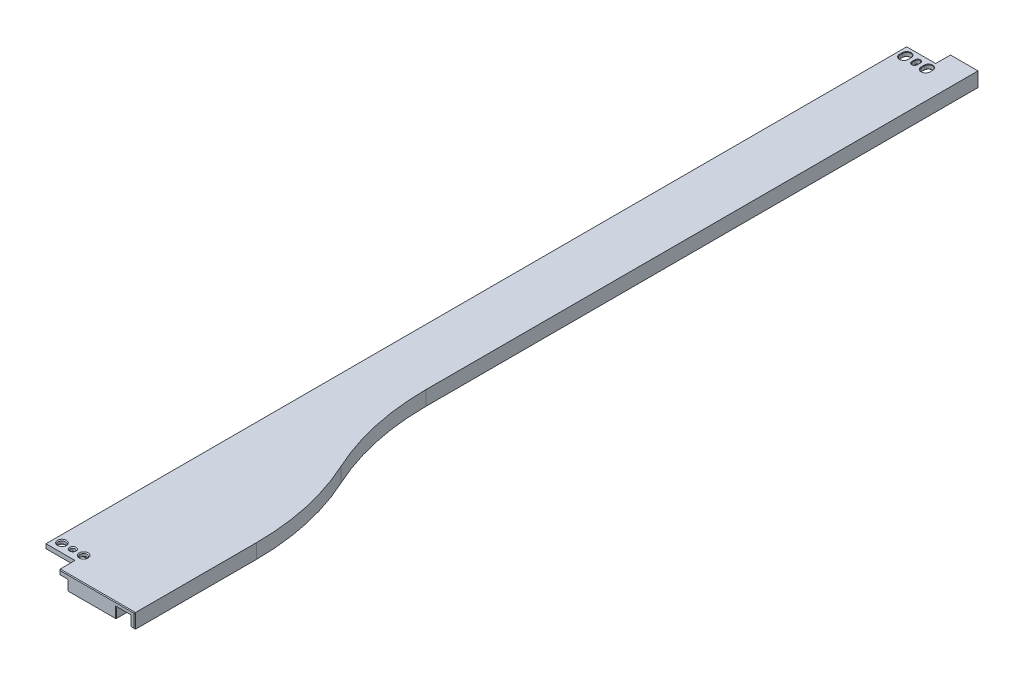
SolidWorks part; units mm, degrees
material "6061 Alloy"
ref_plane "Front" through (0, 0, 0) normal (0, 0, 1) x (1, 0, 0)
ref_plane "Top" through (0, 0, 0) normal (0, 1, 0) x (1, 0, 0)
ref_plane "Right" through (0, 0, 0) normal (1, 0, 0) x (0, 0, -1)
sketch "Sketch1" plane through (0, 0, 0) normal (0, 1, 0) x (1, 0, 0)
  line L0 (0, 0) -> (0, 77.3682) construction
  line L1 (0, 0) -> (-68.6698, 0) construction
  line L2 (-69.1, 0) -> (-69.1, 40) construction
  line L3 (-93.1, 190) -> (-93.1, 840) construction
  line L4 (-126.1, 990) -> (-126.1, 2194) construction
  line L5 (-165.1, 2194) -> (-165.1, 0) construction
  line L6 (-165.1, 2194) -> (-126.1, 2194) construction
  line L7 (-165.1, 0) -> (-69.1, 0) construction
  line L8 (-462.2814, 755.9) -> (800.8337, 755.9) construction
  line L9 (-93.1, 755.6) -> (-145.1, 755.6) construction
  line L10 (-145.1, 755.6) -> (-145.1, 744.9) construction
  line L11 (-145.1, 744.9) -> (-165.1, 744.9) construction
  line L12 (-450.7799, 139.9) -> (404.4044, 139.9) construction
  line L13 (-165.1, 158.4) -> (-145.1, 158.4) construction
  line L14 (-145.1, 158.4) -> (-145.1, 121.4) construction
  line L15 (-145.1, 121.4) -> (-165.1, 121.4) construction
  line L16 (-165.1, 121.4) -> (-165.1, 0) construction
  line L17 (-165.1, 744.9) -> (-165.1, 158.4) construction
  line L18 (-93.1, 755.6) -> (-93.1, 190) construction
  line L19 (-752.0446, 1371.9) -> (535.2926, 1371.9) construction
  line L20 (-878.4617, 1987.9) -> (588.9463, 1987.9) construction
  line L21 (-93.1, 756.2) -> (-145.1, 756.2)
  line L22 (-145.1, 756.2) -> (-145.1, 766.9)
  line L23 (-145.1, 766.9) -> (-165.1, 766.9)
  line L24 (-107.1553, 756.2) -> (-107.1553, 755.6) construction
  line L25 (-144.4764, 1372.2) -> (-144.4764, 1371.6) construction
  line L26 (-126.1, 1371.6) -> (-145.1, 1371.6)
  line L27 (-165.1, 1360.9) -> (-165.1, 766.9)
  line L28 (-126.1, 1371.6) -> (-126.1, 990)
  line L29 (-93.1, 756.2) -> (-93.1, 840)
  line L30 (-145.1, 1371.6) -> (-145.1, 1360.9)
  line L31 (-145.1, 1360.9) -> (-165.1, 1360.9)
  arc A0 (-93.1, 190) -> (-81.1, 115) centre (147.275, 190) ccw construction
  arc A1 (-81.1, 115) -> (-69.1, 40) centre (-309.475, 40) cw construction
  arc A2 (-126.1, 990) -> (-109.6, 915) centre (52.6045, 990) ccw construction
  arc A3 (-109.6, 915) -> (-93.1, 840) centre (-271.8045, 840) cw construction
  arc A4 (-126.1, 990) -> (-109.6, 915) centre (52.6045, 990) ccw
  arc A5 (-109.6, 915) -> (-93.1, 840) centre (-271.8045, 840) cw
  point P28 (-145.1, 139.9)
  point P41 (-107.1553, 755.9)
  point P44 (-144.4764, 1371.9)
  dimension "D1" = 2194
  dimension "D2" = 39
  dimension "D3" = 165.1
  dimension "D4" = 24
  dimension "D5" = 33
  dimension "D6" = 40
  dimension "D7" = 150
  dimension "D8" = 840
  dimension "D9" = 150
  dimension "D10" = 755.9
  dimension "D11" = 0.3
  dimension "D12" = 11
  dimension "D13" = 20
  dimension "D14" = 139.9
  dimension "D15" = 37
  dimension "D16" = 616
  dimension "D17" = 616
extrude "Extrude1" add sketch "Sketch1" against normal blind 10
sketch "Sketch4" plane through (0, -10, 0) normal (0, -1, 0) x (1, 0, 0)
  line L0 (-83.1, 0) -> (-83.1, -40) construction
  line L1 (-107.1, -190) -> (-107.1, -190.4) construction
  line L2 (-100.1, -755.6) -> (-107.1, -755.6) construction
  line L3 (-107.1, -755.6) -> (-107.1, -707.4) construction
  line L6 (-76.1, 0) -> (-76.1, -40) construction
  line L7 (-100.1, -190) -> (-100.1, -755.6) construction
  line L8 (-107.1, -707.4) -> (-165.1, -707.4) construction
  line L10 (-165.1, -707.4) -> (-165.1, -190.4) construction
  line L11 (-165.1, -190.4) -> (-107.1, -190.4) construction
  line L13 (-83.1, 0) -> (-76.1, 0) construction
  line L18 (-165.1, -789.4) -> (-106.1, -789.4)
  line L21 (-165.1, -1360.9) -> (-165.1, -766.9) construction
  line L22 (-96.1, -756.2) -> (-96.1, -840)
  line L23 (-129.1, -990) -> (-129.1, -1371.6)
  line L24 (-96.1, -756.2) -> (-96.1, -840)
  line L25 (-129.1, -990) -> (-129.1, -1371.6)
  line L26 (-106.1, -789.4) -> (-106.1, -756.2)
  line L27 (-96.1, -756.2) -> (-106.1, -756.2)
  line L28 (-93.1, -756.2) -> (-145.1, -756.2) construction
  line L30 (-145.1, -766.9) -> (-165.1, -766.9) construction
  line L31 (-129.1, -1371.6) -> (-139.1, -1371.6)
  line L32 (-139.1, -1371.6) -> (-139.1, -1338.4)
  line L33 (-139.1, -1338.4) -> (-165.1, -1338.4)
  line L34 (-145.1, -1360.9) -> (-165.1, -1360.9) construction
  line L35 (-165.1, -789.4) -> (-165.1, -1338.4)
  arc A0 (-94.6008, -111.8799) -> (-83.1, -40) centre (-313.475, -40) ccw construction
  arc A1 (-94.6008, -111.8799) -> (-107.1, -190) centre (143.275, -190) ccw construction
  arc A6 (-87.9502, -114.064) -> (-76.1, -40) centre (-313.475, -40) ccw construction
  arc A7 (-87.9502, -114.064) -> (-100.1, -190) centre (143.275, -190) ccw construction
  arc A13 (-112.323, -913.7409) -> (-96.1, -840) centre (-271.8045, -840) ccw
  arc A14 (-112.323, -913.7409) -> (-129.1, -990) centre (52.6045, -990) ccw
  arc A15 (-112.323, -913.7409) -> (-96.1, -840) centre (-271.8045, -840) ccw
  arc A16 (-112.323, -913.7409) -> (-129.1, -990) centre (52.6045, -990) ccw
  dimension "D3" = 3
  dimension "D6" = 7
  dimension "D7" = 10
  dimension "D8" = 22.5
  dimension "D9" = 10
  dimension "D10" = 22.5
  dimension "D2" = 7
extrude "Extrude2" cut sketch "Sketch4" against normal offset from surface (7 mm away) 3 up to face at (-132.6, 0, -1023.2909)
sketch "Sketch5" plane through (0, -10, 0) normal (0, -1, 0) x (1, 0, 0)
  line L1 (-165.1, -106.4) -> (-139.1, -106.4) construction
  line L2 (-165.1, -106.4) -> (-165.1, -173.4) construction
  line L3 (-165.1, -173.4) -> (-139.1, -173.4) construction
  line L4 (-139.1, -106.4) -> (-139.1, -173.4) construction
  line L7 (-165.1, -722.4) -> (-139.1, -722.4) construction
  line L8 (-165.1, -722.4) -> (-165.1, -737.4) construction
  line L9 (-165.1, -737.4) -> (-139.1, -737.4) construction
  line L10 (-139.1, -722.4) -> (-139.1, -737.4) construction
  line L11 (-145.1, -766.9) -> (-145.1, -756.2) construction
  line L12 (-165.1, -766.9) -> (-145.1, -766.9)
  line L13 (-165.1, -766.9) -> (-165.1, -781.9)
  line L14 (-165.1, -781.9) -> (-145.1, -781.9)
  line L15 (-145.1, -766.9) -> (-145.1, -781.9)
  line L16 (-139.1, -1338.4) -> (-139.1, -1371.6) construction
  line L17 (-165.1, -1360.9) -> (-139.1, -1360.9)
  line L18 (-165.1, -1360.9) -> (-165.1, -1345.9)
  line L19 (-165.1, -1345.9) -> (-139.1, -1345.9)
  line L20 (-139.1, -1360.9) -> (-139.1, -1345.9)
  dimension "D1" = 67
  dimension "D2" = 15
  dimension "D3" = 15
  dimension "D4" = 15
extrude "Extrude3" cut sketch "Sketch5" against normal up to surface (7 mm away) up to face at (-125.7691, -3, -1023.1737)
sketch "Sketch15" plane through (0, -10, 0) normal (0, -1, 0) x (1, 0, 0)
  line L0 (-145.1, -781.9) -> (-165.1, -781.9) construction
  line L1 (-139.1, -1360.9) -> (-145.1, -1360.9)
  line L2 (-139.1, -1360.9) -> (-139.1, -1371.6)
  line L3 (-139.1, -1371.6) -> (-145.1, -1371.6)
  line L4 (-145.1, -1360.9) -> (-145.1, -1371.6)
  line L5 (-145.1, -756.2) -> (-139.1, -756.2)
  line L6 (-145.1, -756.2) -> (-145.1, -781.9)
  line L7 (-145.1, -781.9) -> (-139.1, -781.9)
  line L8 (-139.1, -756.2) -> (-139.1, -781.9)
extrude "Extrude9" cut sketch "Sketch15" against normal up to surface (7 mm away) up to face at (-133.56, -3, -1126.8382)
sketch "Sketch8" plane through (0, -3, 0) normal (0, -1, 0) x (1, 0, 0)
  line L0 (-450.7799, -139.9) -> (404.4044, -139.9) construction
  line L1 (-161.3213, -115.4) -> (-146.3213, -115.4) construction
  line L2 (-161.3213, -115.4) -> (-161.3213, -164.4) construction
  line L3 (-161.3213, -164.4) -> (-146.3213, -164.4) construction
  line L4 (-146.3213, -115.4) -> (-146.3213, -164.4) construction
  line L6 (-165.1, -781.9) -> (-165.1, -766.9) construction
  line L7 (-146.3213, -755.9) -> (-160.1, -755.9) construction
  line L8 (-146.3213, -755.9) -> (-146.3213, -731.4) construction
  line L9 (-146.3213, -731.4) -> (-160.1, -731.4) construction
  line L10 (-160.1, -755.9) -> (-160.1, -731.4) construction
  line L12 (-160.1, -755.9) -> (-145.1, -755.9)
  line L13 (-160.1, -755.9) -> (-160.1, -772.9)
  line L14 (-160.1, -772.9) -> (-145.1, -772.9)
  line L15 (-145.1, -755.9) -> (-145.1, -772.9)
  line L17 (-462.2814, -755.9) -> (800.8337, -755.9) construction
  line L19 (-752.0446, -1371.9) -> (535.2926, -1371.9) construction
  line L20 (-160.1, -1371.9) -> (-145.1, -1371.9)
  line L21 (-160.1, -1371.9) -> (-160.1, -1354.9)
  line L22 (-160.1, -1354.9) -> (-145.1, -1354.9)
  line L23 (-145.1, -1371.9) -> (-145.1, -1354.9)
  point P4 (-161.3213, -139.9)
  point P9 (-153.8213, -115.4)
  point P10 (-153.8213, -164.4)
  point P17 (-153.2106, -731.4)
  point P23 (-152.6, -772.9)
  point P28 (-152.6, -1354.9)
  dimension "D1" = 5
  dimension "D2" = 15
  dimension "D3" = 49
  dimension "D4" = 24.5
  dimension "D5" = 17
  dimension "D6" = 15
hole_wizard "1/8 (0.125) Diameter Hole1" positions "3DSketch1" profile "Sketch9" hole size "1/8" standard "Ansi Inch" end condition through all
sketch3d "3DSketch1"
  point P0 (-152.6, -3, -772.9)
sketch "Sketch9" plane through (-152.6, -3, -772.9) normal (1, 0, 0) x (0, 0, -1)
  line L0 (0, 0) -> (0, 3)
  line L1 (0, 3) -> (2.2479, 3)
  line L2 (1.6129, 2.365) -> (1.6129, 0.635)
  line L3 (1.6129, 0.635) -> (2.2479, 0)
  line L5 (2.2479, 0) -> (0, 0)
  line L6 (-1.6129, 0.635) -> (-2.2479, 0) construction
  line L7 (2.2479, 3) -> (1.6129, 2.365)
  line L8 (-2.2479, 3) -> (-1.6129, 2.365) construction
  line L11 (0, -6.35) -> (0, 107.95) construction
  dimension "Thru Hole Dia." = 3.2258
  dimension "Thru Hole Depth" = 3
  dimension "Near C'Sink Dia." = 4.4958
  dimension "Near C'Sink Angle" = 90
  dimension "Far C'Sink Dia." = 4.4958
  dimension "Far C'Sink Angle" = 90
hole_wizard "#8 Clearance Hole1" positions "3DSketch2" profile "Sketch10" hole size "#8" standard "Ansi Inch" end condition through all
sketch3d "3DSketch2"
  point P0 (-160.1, -3, -772.9)
  point P3 (-145.1, -3, -772.9)
sketch "Sketch10" plane through (-160.1, -3, -772.9) normal (1, 0, 0) x (0, 0, -1)
  line L0 (0, 0) -> (0, 3)
  line L1 (0, 3) -> (3.0924, 3)
  line L2 (2.4574, 2.365) -> (2.4574, 0.635)
  line L3 (2.4574, 0.635) -> (3.0924, 0)
  line L5 (3.0924, 0) -> (0, 0)
  line L6 (-2.4574, 0.635) -> (-3.0924, 0) construction
  line L7 (3.0924, 3) -> (2.4574, 2.365)
  line L8 (-3.0924, 3) -> (-2.4575, 2.365) construction
  line L11 (0, -6.35) -> (0, 107.95) construction
  dimension "Thru Hole Dia." = 4.9149
  dimension "Thru Hole Depth" = 3
  dimension "Near C'Sink Dia." = 6.1849
  dimension "Near C'Sink Angle" = 90
  dimension "Far C'Sink Dia." = 6.1849
  dimension "Far C'Sink Angle" = 90
sketch "Sketch12" plane through (0, -3, 0) normal (0, -1, 0) x (1, 0, 0)
  line L0 (-153.2106, -730.4) -> (-153.2106, -732.4) construction
  line L1 (-154.8616, -730.4) -> (-151.5596, -730.4) construction
  line L2 (-154.8616, -730.4) -> (-154.8616, -732.4) construction
  line L3 (-154.8616, -732.4) -> (-151.5596, -732.4) construction
  line L4 (-151.5596, -730.4) -> (-151.5596, -732.4) construction
  line L5 (-152.6, -1353.9) -> (-152.6, -1355.9) construction
  line L6 (-154.251, -1353.9) -> (-150.949, -1353.9) construction
  line L7 (-154.251, -1353.9) -> (-154.251, -1355.9)
  line L8 (-154.251, -1355.9) -> (-150.949, -1355.9) construction
  line L9 (-150.949, -1353.9) -> (-150.949, -1355.9)
  line L10 (-146.3213, -731.4) -> (-160.1, -731.4) construction
  line L11 (-145.1, -1353.9) -> (-145.1, -1355.9) construction
  line L12 (-142.35, -1353.9) -> (-142.35, -1355.9)
  line L13 (-147.85, -1353.9) -> (-147.85, -1355.9)
  line L14 (-160.1, -1353.9) -> (-160.1, -1355.9) construction
  line L15 (-162.85, -1353.9) -> (-162.85, -1355.9)
  line L16 (-157.35, -1353.9) -> (-157.35, -1355.9)
  arc A0 (-151.5596, -730.4) -> (-154.8616, -730.4) centre (-153.2106, -730.4) ccw construction
  arc A1 (-154.8616, -732.4) -> (-151.5596, -732.4) centre (-153.2106, -732.4) ccw construction
  arc A2 (-150.949, -1353.9) -> (-154.251, -1353.9) centre (-152.6, -1353.9) ccw
  arc A3 (-154.251, -1355.9) -> (-150.949, -1355.9) centre (-152.6, -1355.9) ccw
  arc A4 (-142.35, -1353.9) -> (-147.85, -1353.9) centre (-145.1, -1353.9) ccw
  arc A5 (-147.85, -1355.9) -> (-142.35, -1355.9) centre (-145.1, -1355.9) ccw
  arc A6 (-162.85, -1353.9) -> (-157.35, -1353.9) centre (-160.1, -1353.9) cw
  arc A7 (-157.35, -1355.9) -> (-162.85, -1355.9) centre (-160.1, -1355.9) cw
  point P14 (-152.6, -1354.9)
  point P19 (-153.2106, -731.4)
  point P20 (-153.2106, -731.4)
  point P21 (-145.1, -1354.9)
  point P29 (-160.1, -1354.9)
  dimension "D6" = 2
  dimension "D1" = 3.302
  dimension "D2" = 2
  dimension "D3" = 3.302
  dimension "D4" = 2
  dimension "D5" = 5.5
extrude "Extrude6" cut sketch "Sketch12" against normal through all
sketch "Sketch14" plane through (0, -10, 0) normal (0, -1, 0) x (1, 0, 0)
  line L0 (-145.1, -781.9) -> (-145.1, -756.2) construction
  line L1 (-165.1, -781.9) -> (-139.1, -781.9) construction
  circle A0 centre (-145.1, -780.3125) radius 1.5875
  dimension "D1" = 3.175
extrude "Extrude8" [suppressed] cut sketch "Sketch14" against normal up to surface (7 mm away)
sketch "Sketch16" plane through (0, -10, 0) normal (0, -1, 0) x (1, 0, 0)
  line L0 (-165.1, -781.9) -> (-139.1, -781.9) construction
  line L1 (-139.1, -781.9) -> (-139.1, -756.2) construction
  circle A0 centre (-139.1, -780.3125) radius 1.5875
  dimension "D1" = 3.175
extrude "Extrude10" cut sketch "Sketch16" against normal up to surface (7 mm away) up to face at (-160.1, -3, -775.9925)
chamfer "Chamfer1" distance 0.3 angle 45 8 edges at (-150.949, 0, -1354.9) (-152.6, 0, -1352.249) (-154.251, 0, -1354.9) (-152.6, 0, -1357.551) (-152.6, -3, -1357.551) (-154.251, -3, -1354.9) (-152.6, -3, -1352.249) (-150.949, -3, -1354.9)
chamfer "Chamfer2" distance 0.5 angle 45 13 edges at (-94.6, -10, -756.2) (-93.1, -5, -756.2) (-119.1, 0, -756.2) (-145.1, -1.5, -756.2) (-106.1, -6.5, -756.2) (-101.1, -3, -756.2) (-96.1, -6.5, -756.2) (-126.1, -5, -1371.6) (-127.6, -10, -1371.6) (-129.1, -6.5, -1371.6) (-137.1, -3, -1371.6) (-145.1, -1.5, -1371.6) (-135.6, 0, -1371.6)
chamfer "Chamfer3" distance 0.3 angle 45 16 edges at (-157.35, -3, -1354.9) (-157.35, 0, -1354.9) (-160.1, -3, -1351.15) (-160.1, 0, -1351.15) (-162.85, -3, -1354.9) (-162.85, 0, -1354.9) (-160.1, -3, -1358.65) (-160.1, 0, -1358.65) (-142.35, 0, -1354.9) (-145.1, 0, -1351.15) (-147.85, 0, -1354.9) (-145.1, 0, -1358.65) (-142.35, -3, -1354.9) (-145.1, -3, -1351.15) (-147.85, -3, -1354.9) (-145.1, -3, -1358.65)
fillet "Fillet3" radius 3 3 edges at (-139.1, -6.5, -1338.4) (-139.1, -6.5, -1345.9) (-106.1, -6.5, -789.4)
fillet "Fillet2" radius 0.5 15 edges at (-137.5125, -3, -780.3125) (-96.1, -3, -798.35) (-100.2037, -3, -877.7522) (-124.8562, -3, -950.9586) (-139.1, -3, -767.4625) (-152.1, -3, -781.9) (-153.6, -3, -1345.9) (-129.1, -3, -1180.55) (-153.6, -3, -1338.4) (-137.1, -3, -789.4) (-106.1, -3, -771.55) (-106.9787, -3, -788.5213) (-139.9787, -3, -1339.2787) (-139.1, -3, -1342.15) (-139.9787, -3, -1345.0213)
